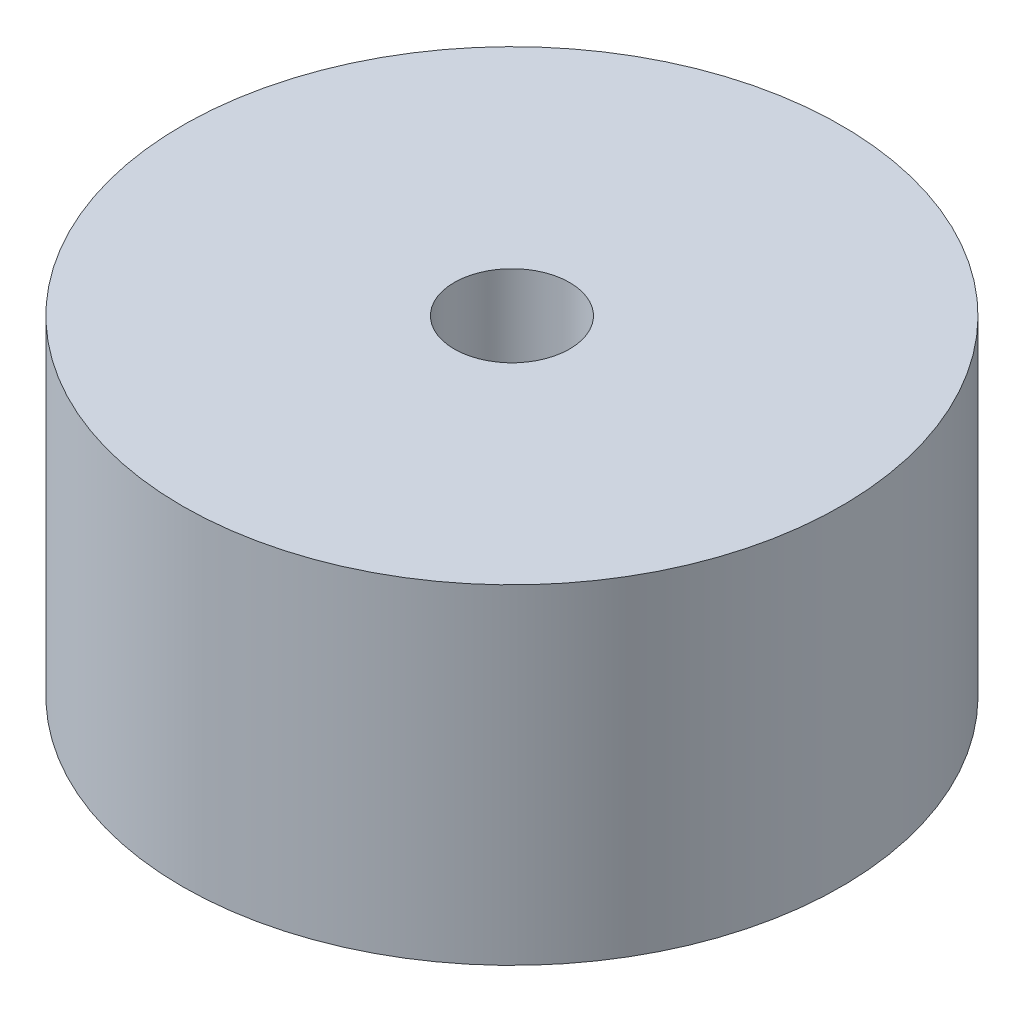
SolidWorks part; units mm, degrees
ref_plane "Front Plane" through (0, 0, 0) normal (0, 0, 1) x (1, 0, 0)
ref_plane "Top Plane" through (0, 0, 0) normal (0, 1, 0) x (1, 0, 0)
ref_plane "Right Plane" through (0, 0, 0) normal (1, 0, 0) x (0, 0, -1)
sketch "Sketch1" plane through (0, 0, 0) normal (0, 1, 0) x (1, 0, 0)
  circle A0 centre (0, 0) radius 10
  circle A1 centre (0, 0) radius 1.75
  dimension "D1" = 20
  dimension "D2" = 3.5
extrude "Boss-Extrude1" add sketch "Sketch1" along normal blind 10
sketch "Sketch2" plane through (0, 0, 0) normal (0, -1, 0) x (1, 0, 0)
  circle A0 centre (0, 0) radius 3.2
  dimension "D1" = 6.4
extrude "Cut-Extrude1" cut sketch "Sketch2" against normal blind 5
